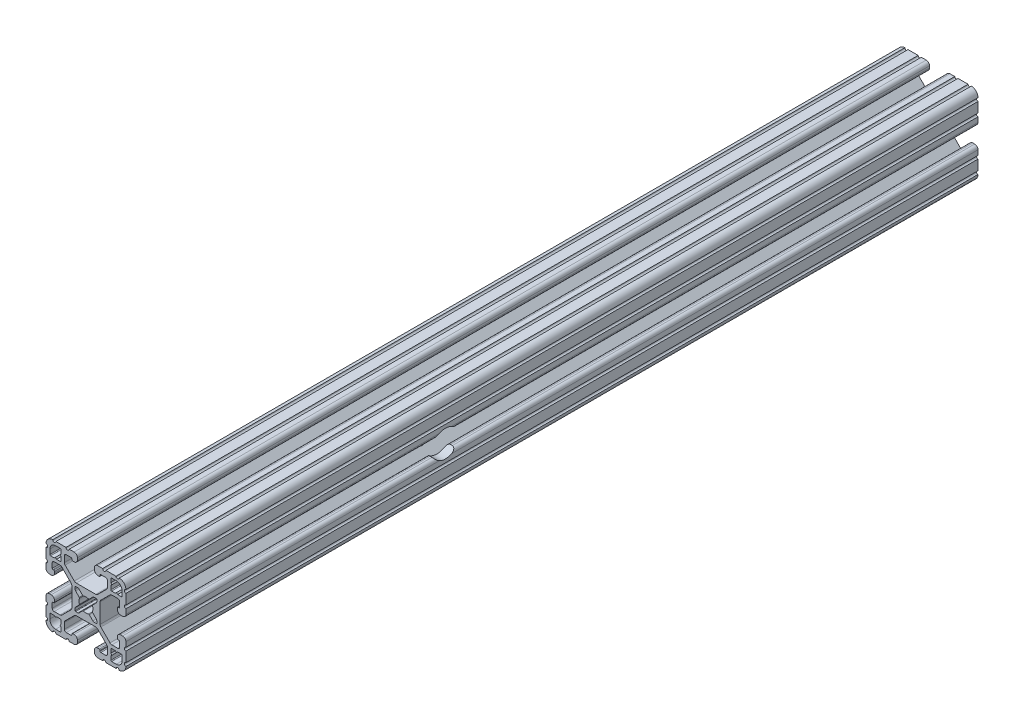
SolidWorks part; units mm, degrees
ref_plane "Front Plane" through (0, 0, 0) normal (0, 0, 1) x (1, 0, 0)
ref_plane "Top Plane" through (0, 0, 0) normal (0, 1, 0) x (1, 0, 0)
ref_plane "Right Plane" through (0, 0, 0) normal (1, 0, 0) x (0, 0, -1)
ref_plane "Plane1" through (0, 0, -2322.576) normal (0, 0, -1) x (-1, 0, 0)
sketch "Sketch1" plane through (0, 0, -2322.576) normal (0, 0, -1) x (-1, 0, 0)
  line L0 (17.2466, 14.4526) -> (17.2466, 12.2428)
  line L1 (16.8656, 11.8618) -> (15.0927, 11.8618)
  line L2 (15.0927, 11.8618) -> (14.5542, 12.4003)
  line L3 (14.5542, 12.4003) -> (14.0157, 11.8618)
  line L4 (14.0157, 11.8618) -> (12.2428, 11.8618)
  line L5 (11.8618, 12.2428) -> (11.8618, 14.0157)
  line L6 (11.8618, 14.0157) -> (12.4003, 14.5542)
  line L7 (12.4003, 14.5542) -> (11.8618, 15.0927)
  line L8 (11.8618, 15.0927) -> (11.8618, 16.8656)
  line L9 (12.2428, 17.2466) -> (14.4526, 17.2466)
  line L10 (17.2466, -12.2428) -> (17.2466, -14.4526)
  line L11 (14.4526, -17.2466) -> (12.2428, -17.2466)
  line L12 (11.8618, -16.8656) -> (11.8618, -15.0927)
  line L13 (11.8618, -15.0927) -> (12.4003, -14.5542)
  line L14 (12.4003, -14.5542) -> (11.8618, -14.0157)
  line L15 (11.8618, -14.0157) -> (11.8618, -12.2428)
  line L16 (12.2428, -11.8618) -> (14.0157, -11.8618)
  line L17 (14.0157, -11.8618) -> (14.5542, -12.4003)
  line L18 (14.5542, -12.4003) -> (15.0927, -11.8618)
  line L19 (15.0927, -11.8618) -> (16.8656, -11.8618)
  line L20 (5.1689, -3.9207) -> (5.1689, -4.9149)
  line L21 (4.9149, -5.1689) -> (3.9207, -5.1689)
  line L22 (3.2921, -4.9085) -> (1.5823, -3.1988)
  line L23 (-1.5823, -3.1988) -> (-3.2921, -4.9085)
  line L24 (-3.9207, -5.1689) -> (-4.9149, -5.1689)
  line L25 (-5.1689, -4.9149) -> (-5.1689, -3.9207)
  line L26 (-4.9085, -3.2921) -> (-3.1988, -1.5823)
  line L27 (-3.1988, 1.5823) -> (-4.9085, 3.2921)
  line L28 (-5.1689, 3.9207) -> (-5.1689, 4.9149)
  line L29 (-4.9149, 5.1689) -> (-3.9207, 5.1689)
  line L30 (-3.2921, 4.9085) -> (-1.5823, 3.1988)
  line L31 (1.5823, 3.1988) -> (3.2921, 4.9085)
  line L32 (3.9207, 5.1689) -> (4.9149, 5.1689)
  line L33 (5.1689, 4.9149) -> (5.1689, 3.9207)
  line L34 (4.9085, 3.2921) -> (3.1988, 1.5823)
  line L35 (3.1988, -1.5823) -> (4.9085, -3.2921)
  line L36 (-11.8618, -12.2428) -> (-11.8618, -14.0157)
  line L37 (-11.8618, -14.0157) -> (-12.4003, -14.5542)
  line L38 (-12.4003, -14.5542) -> (-11.8618, -15.0927)
  line L39 (-11.8618, -15.0927) -> (-11.8618, -16.8656)
  line L40 (-12.2428, -17.2466) -> (-14.4526, -17.2466)
  line L41 (-17.2466, -14.4526) -> (-17.2466, -12.2428)
  line L42 (-16.8656, -11.8618) -> (-15.0927, -11.8618)
  line L43 (-15.0927, -11.8618) -> (-14.5542, -12.4003)
  line L44 (-14.5542, -12.4003) -> (-14.0157, -11.8618)
  line L45 (-14.0157, -11.8618) -> (-12.2428, -11.8618)
  line L46 (-11.8618, 16.8656) -> (-11.8618, 15.0927)
  line L47 (-11.8618, 15.0927) -> (-12.4003, 14.5542)
  line L48 (-12.4003, 14.5542) -> (-11.8618, 14.0157)
  line L49 (-11.8618, 14.0157) -> (-11.8618, 12.2428)
  line L50 (-12.2428, 11.8618) -> (-14.0157, 11.8618)
  line L51 (-14.0157, 11.8618) -> (-14.5542, 12.4003)
  line L52 (-14.5542, 12.4003) -> (-15.0927, 11.8618)
  line L53 (-15.0927, 11.8618) -> (-16.8656, 11.8618)
  line L54 (-17.2466, 12.2428) -> (-17.2466, 14.4526)
  line L55 (-14.4526, 17.2466) -> (-12.2428, 17.2466)
  line L56 (19.05, -14.3256) -> (19.05, -9.4996)
  line L57 (19.05, -7.9756) -> (19.05, -5.6388)
  line L58 (17.4752, -4.064) -> (16.5608, -4.064)
  line L59 (14.986, -5.6388) -> (14.986, -6.35)
  line L60 (15.367, -6.731) -> (15.6972, -6.731)
  line L61 (16.0782, -7.112) -> (16.0782, -9.398)
  line L62 (15.1892, -10.287) -> (12.3756, -10.287)
  line L63 (11.4776, -9.915) -> (7.1157, -5.5531)
  line L64 (6.7437, -4.6551) -> (6.7437, 4.6551)
  line L65 (7.1157, 5.5531) -> (11.4776, 9.915)
  line L66 (12.3756, 10.287) -> (15.1892, 10.287)
  line L67 (16.0782, 9.398) -> (16.0782, 7.112)
  line L68 (15.6972, 6.731) -> (15.367, 6.731)
  line L69 (14.986, 6.35) -> (14.986, 5.6388)
  line L70 (16.5608, 4.064) -> (17.4752, 4.064)
  line L71 (19.05, 5.6388) -> (19.05, 7.9756)
  line L72 (19.05, 9.4996) -> (19.05, 14.3256)
  line L73 (14.3256, 19.05) -> (9.4996, 19.05)
  line L74 (7.9756, 19.05) -> (5.6388, 19.05)
  line L75 (4.064, 17.4752) -> (4.064, 16.5608)
  line L76 (5.6388, 14.986) -> (6.35, 14.986)
  line L77 (6.731, 15.367) -> (6.731, 15.6972)
  line L78 (7.112, 16.0782) -> (9.398, 16.0782)
  line L79 (10.287, 15.1892) -> (10.287, 12.3756)
  line L80 (9.915, 11.4776) -> (5.5531, 7.1157)
  line L81 (4.6551, 6.7437) -> (-4.6551, 6.7437)
  line L82 (-5.5531, 7.1157) -> (-9.915, 11.4776)
  line L83 (-10.287, 12.3756) -> (-10.287, 15.1892)
  line L84 (-9.398, 16.0782) -> (-7.112, 16.0782)
  line L85 (-6.731, 15.6972) -> (-6.731, 15.367)
  line L86 (-6.35, 14.986) -> (-5.6388, 14.986)
  line L87 (-4.064, 16.5608) -> (-4.064, 17.4752)
  line L88 (-5.6388, 19.05) -> (-7.9756, 19.05)
  line L89 (-9.4996, 19.05) -> (-14.3256, 19.05)
  line L90 (-19.05, 14.3256) -> (-19.05, 9.4996)
  line L91 (-19.05, 7.9756) -> (-19.05, 5.6388)
  line L92 (-17.4752, 4.064) -> (-16.5608, 4.064)
  line L93 (-14.986, 5.6388) -> (-14.986, 6.35)
  line L94 (-15.367, 6.731) -> (-15.6972, 6.731)
  line L95 (-16.0782, 7.112) -> (-16.0782, 9.398)
  line L96 (-15.1892, 10.287) -> (-12.3756, 10.287)
  line L97 (-11.4776, 9.915) -> (-7.1157, 5.5531)
  line L98 (-6.7437, 4.6551) -> (-6.7437, -4.6551)
  line L99 (-7.1157, -5.5531) -> (-11.4776, -9.915)
  line L100 (-12.3756, -10.287) -> (-15.1892, -10.287)
  line L101 (-16.0782, -9.398) -> (-16.0782, -7.112)
  line L102 (-15.6972, -6.731) -> (-15.367, -6.731)
  line L103 (-14.986, -6.35) -> (-14.986, -5.6388)
  line L104 (-16.5608, -4.064) -> (-17.4752, -4.064)
  line L105 (-19.05, -5.6388) -> (-19.05, -7.9756)
  line L106 (-19.05, -9.4996) -> (-19.05, -14.3256)
  line L107 (-14.3256, -19.05) -> (-9.4996, -19.05)
  line L108 (-7.9756, -19.05) -> (-5.6388, -19.05)
  line L109 (-4.064, -17.4752) -> (-4.064, -16.5608)
  line L110 (-5.6388, -14.986) -> (-6.35, -14.986)
  line L111 (-6.731, -15.367) -> (-6.731, -15.6972)
  line L112 (-7.112, -16.0782) -> (-9.398, -16.0782)
  line L113 (-10.287, -15.1892) -> (-10.287, -12.3756)
  line L114 (-9.915, -11.4776) -> (-5.5531, -7.1157)
  line L115 (-4.6551, -6.7437) -> (4.6551, -6.7437)
  line L116 (5.5531, -7.1157) -> (9.915, -11.4776)
  line L117 (10.287, -12.3756) -> (10.287, -15.1892)
  line L118 (9.398, -16.0782) -> (7.112, -16.0782)
  line L119 (6.731, -15.6972) -> (6.731, -15.367)
  line L120 (6.35, -14.986) -> (5.6388, -14.986)
  line L121 (4.064, -16.5608) -> (4.064, -17.4752)
  line L122 (5.6388, -19.05) -> (7.9756, -19.05)
  line L123 (9.4996, -19.05) -> (14.3256, -19.05)
  arc A0 (17.2466, 12.2428) -> (16.8656, 11.8618) centre (16.8656, 12.2428) cw
  arc A1 (12.2428, 11.8618) -> (11.8618, 12.2428) centre (12.2428, 12.2428) cw
  arc A2 (11.8618, 16.8656) -> (12.2428, 17.2466) centre (12.2428, 16.8656) cw
  arc A3 (14.4526, 17.2466) -> (17.2466, 14.4526) centre (14.4526, 14.4526) cw
  arc A4 (17.2466, -14.4526) -> (14.4526, -17.2466) centre (14.4526, -14.4526) cw
  arc A5 (12.2428, -17.2466) -> (11.8618, -16.8656) centre (12.2428, -16.8656) cw
  arc A6 (11.8618, -12.2428) -> (12.2428, -11.8618) centre (12.2428, -12.2428) cw
  arc A7 (16.8656, -11.8618) -> (17.2466, -12.2428) centre (16.8656, -12.2428) cw
  arc A8 (5.1689, -4.9149) -> (4.9149, -5.1689) centre (4.9149, -4.9149) cw
  arc A9 (3.9207, -5.1689) -> (3.2921, -4.9085) centre (3.9207, -4.2799) cw
  arc A10 (1.5823, -3.1988) -> (1.178, -3.1119) centre (1.3129, -3.4682) ccw
  arc A11 (1.178, -3.1119) -> (-1.178, -3.1119) centre (0, 0) cw
  arc A12 (-1.178, -3.1119) -> (-1.5823, -3.1988) centre (-1.3129, -3.4682) ccw
  arc A13 (-3.2921, -4.9085) -> (-3.9207, -5.1689) centre (-3.9207, -4.2799) cw
  arc A14 (-4.9149, -5.1689) -> (-5.1689, -4.9149) centre (-4.9149, -4.9149) cw
  arc A15 (-5.1689, -3.9207) -> (-4.9085, -3.2921) centre (-4.2799, -3.9207) cw
  arc A16 (-3.1988, -1.5823) -> (-3.1119, -1.178) centre (-3.4682, -1.3129) ccw
  arc A17 (-3.1119, -1.178) -> (-3.1119, 1.178) centre (0, 0) cw
  arc A18 (-3.1119, 1.178) -> (-3.1988, 1.5823) centre (-3.4682, 1.3129) ccw
  arc A19 (-4.9085, 3.2921) -> (-5.1689, 3.9207) centre (-4.2799, 3.9207) cw
  arc A20 (-5.1689, 4.9149) -> (-4.9149, 5.1689) centre (-4.9149, 4.9149) cw
  arc A21 (-3.9207, 5.1689) -> (-3.2921, 4.9085) centre (-3.9207, 4.2799) cw
  arc A22 (-1.5823, 3.1988) -> (-1.178, 3.1119) centre (-1.3129, 3.4682) ccw
  arc A23 (-1.178, 3.1119) -> (1.178, 3.1119) centre (0, 0) cw
  arc A24 (1.178, 3.1119) -> (1.5823, 3.1988) centre (1.3129, 3.4682) ccw
  arc A25 (3.2921, 4.9085) -> (3.9207, 5.1689) centre (3.9207, 4.2799) cw
  arc A26 (4.9149, 5.1689) -> (5.1689, 4.9149) centre (4.9149, 4.9149) cw
  arc A27 (5.1689, 3.9207) -> (4.9085, 3.2921) centre (4.2799, 3.9207) cw
  arc A28 (3.1988, 1.5823) -> (3.1119, 1.178) centre (3.4682, 1.3129) ccw
  arc A29 (3.1119, 1.178) -> (3.1119, -1.178) centre (0, 0) cw
  arc A30 (3.1119, -1.178) -> (3.1988, -1.5823) centre (3.4682, -1.3129) ccw
  arc A31 (4.9085, -3.2921) -> (5.1689, -3.9207) centre (4.2799, -3.9207) cw
  arc A32 (-11.8618, -16.8656) -> (-12.2428, -17.2466) centre (-12.2428, -16.8656) cw
  arc A33 (-14.4526, -17.2466) -> (-17.2466, -14.4526) centre (-14.4526, -14.4526) cw
  arc A34 (-17.2466, -12.2428) -> (-16.8656, -11.8618) centre (-16.8656, -12.2428) cw
  arc A35 (-12.2428, -11.8618) -> (-11.8618, -12.2428) centre (-12.2428, -12.2428) cw
  arc A36 (-12.2428, 17.2466) -> (-11.8618, 16.8656) centre (-12.2428, 16.8656) cw
  arc A37 (-11.8618, 12.2428) -> (-12.2428, 11.8618) centre (-12.2428, 12.2428) cw
  arc A38 (-16.8656, 11.8618) -> (-17.2466, 12.2428) centre (-16.8656, 12.2428) cw
  arc A39 (-17.2466, 14.4526) -> (-14.4526, 17.2466) centre (-14.4526, 14.4526) cw
  arc A40 (19.05, -9.4996) -> (19.05, -7.9756) centre (19.05, -8.7376) cw
  arc A41 (19.05, -5.6388) -> (17.4752, -4.064) centre (17.4752, -5.6388) ccw
  arc A42 (16.5608, -4.064) -> (14.986, -5.6388) centre (16.5608, -5.6388) ccw
  arc A43 (14.986, -6.35) -> (15.367, -6.731) centre (15.367, -6.35) ccw
  arc A44 (15.6972, -6.731) -> (16.0782, -7.112) centre (15.6972, -7.112) cw
  arc A45 (16.0782, -9.398) -> (15.1892, -10.287) centre (15.1892, -9.398) cw
  arc A46 (12.3756, -10.287) -> (11.4776, -9.915) centre (12.3756, -9.017) cw
  arc A47 (7.1157, -5.5531) -> (6.7437, -4.6551) centre (8.0137, -4.6551) cw
  arc A48 (6.7437, 4.6551) -> (7.1157, 5.5531) centre (8.0137, 4.6551) cw
  arc A49 (11.4776, 9.915) -> (12.3756, 10.287) centre (12.3756, 9.017) cw
  arc A50 (15.1892, 10.287) -> (16.0782, 9.398) centre (15.1892, 9.398) cw
  arc A51 (16.0782, 7.112) -> (15.6972, 6.731) centre (15.6972, 7.112) cw
  arc A52 (15.367, 6.731) -> (14.986, 6.35) centre (15.367, 6.35) ccw
  arc A53 (14.986, 5.6388) -> (16.5608, 4.064) centre (16.5608, 5.6388) ccw
  arc A54 (17.4752, 4.064) -> (19.05, 5.6388) centre (17.4752, 5.6388) ccw
  arc A55 (19.05, 7.9756) -> (19.05, 9.4996) centre (19.05, 8.7376) cw
  arc A56 (19.05, 14.3256) -> (19.0499, 15.8496) centre (19.05, 15.0876) cw
  arc A57 (19.0499, 15.8496) -> (15.8496, 19.0499) centre (15.875, 15.875) ccw
  arc A58 (15.8496, 19.0499) -> (14.3256, 19.05) centre (15.0876, 19.05) cw
  arc A59 (9.4996, 19.05) -> (7.9756, 19.05) centre (8.7376, 19.05) cw
  arc A60 (5.6388, 19.05) -> (4.064, 17.4752) centre (5.6388, 17.4752) ccw
  arc A61 (4.064, 16.5608) -> (5.6388, 14.986) centre (5.6388, 16.5608) ccw
  arc A62 (6.35, 14.986) -> (6.731, 15.367) centre (6.35, 15.367) ccw
  arc A63 (6.731, 15.6972) -> (7.112, 16.0782) centre (7.112, 15.6972) cw
  arc A64 (9.398, 16.0782) -> (10.287, 15.1892) centre (9.398, 15.1892) cw
  arc A65 (10.287, 12.3756) -> (9.915, 11.4776) centre (9.017, 12.3756) cw
  arc A66 (5.5531, 7.1157) -> (4.6551, 6.7437) centre (4.6551, 8.0137) cw
  arc A67 (-4.6551, 6.7437) -> (-5.5531, 7.1157) centre (-4.6551, 8.0137) cw
  arc A68 (-9.915, 11.4776) -> (-10.287, 12.3756) centre (-9.017, 12.3756) cw
  arc A69 (-10.287, 15.1892) -> (-9.398, 16.0782) centre (-9.398, 15.1892) cw
  arc A70 (-7.112, 16.0782) -> (-6.731, 15.6972) centre (-7.112, 15.6972) cw
  arc A71 (-6.731, 15.367) -> (-6.35, 14.986) centre (-6.35, 15.367) ccw
  arc A72 (-5.6388, 14.986) -> (-4.064, 16.5608) centre (-5.6388, 16.5608) ccw
  arc A73 (-4.064, 17.4752) -> (-5.6388, 19.05) centre (-5.6388, 17.4752) ccw
  arc A74 (-7.9756, 19.05) -> (-9.4996, 19.05) centre (-8.7376, 19.05) cw
  arc A75 (-14.3256, 19.05) -> (-15.8496, 19.0499) centre (-15.0876, 19.05) cw
  arc A76 (-15.8496, 19.0499) -> (-19.0499, 15.8496) centre (-15.875, 15.875) ccw
  arc A77 (-19.0499, 15.8496) -> (-19.05, 14.3256) centre (-19.05, 15.0876) cw
  arc A78 (-19.05, 9.4996) -> (-19.05, 7.9756) centre (-19.05, 8.7376) cw
  arc A79 (-19.05, 5.6388) -> (-17.4752, 4.064) centre (-17.4752, 5.6388) ccw
  arc A80 (-16.5608, 4.064) -> (-14.986, 5.6388) centre (-16.5608, 5.6388) ccw
  arc A81 (-14.986, 6.35) -> (-15.367, 6.731) centre (-15.367, 6.35) ccw
  arc A82 (-15.6972, 6.731) -> (-16.0782, 7.112) centre (-15.6972, 7.112) cw
  arc A83 (-16.0782, 9.398) -> (-15.1892, 10.287) centre (-15.1892, 9.398) cw
  arc A84 (-12.3756, 10.287) -> (-11.4776, 9.915) centre (-12.3756, 9.017) cw
  arc A85 (-7.1157, 5.5531) -> (-6.7437, 4.6551) centre (-8.0137, 4.6551) cw
  arc A86 (-6.7437, -4.6551) -> (-7.1157, -5.5531) centre (-8.0137, -4.6551) cw
  arc A87 (-11.4776, -9.915) -> (-12.3756, -10.287) centre (-12.3756, -9.017) cw
  arc A88 (-15.1892, -10.287) -> (-16.0782, -9.398) centre (-15.1892, -9.398) cw
  arc A89 (-16.0782, -7.112) -> (-15.6972, -6.731) centre (-15.6972, -7.112) cw
  arc A90 (-15.367, -6.731) -> (-14.986, -6.35) centre (-15.367, -6.35) ccw
  arc A91 (-14.986, -5.6388) -> (-16.5608, -4.064) centre (-16.5608, -5.6388) ccw
  arc A92 (-17.4752, -4.064) -> (-19.05, -5.6388) centre (-17.4752, -5.6388) ccw
  arc A93 (-19.05, -7.9756) -> (-19.05, -9.4996) centre (-19.05, -8.7376) cw
  arc A94 (-19.05, -14.3256) -> (-19.0499, -15.8496) centre (-19.05, -15.0876) cw
  arc A95 (-19.0499, -15.8496) -> (-15.8496, -19.0499) centre (-15.875, -15.875) ccw
  arc A96 (-15.8496, -19.0499) -> (-14.3256, -19.05) centre (-15.0876, -19.05) cw
  arc A97 (-9.4996, -19.05) -> (-7.9756, -19.05) centre (-8.7376, -19.05) cw
  arc A98 (-5.6388, -19.05) -> (-4.064, -17.4752) centre (-5.6388, -17.4752) ccw
  arc A99 (-4.064, -16.5608) -> (-5.6388, -14.986) centre (-5.6388, -16.5608) ccw
  arc A100 (-6.35, -14.986) -> (-6.731, -15.367) centre (-6.35, -15.367) ccw
  arc A101 (-6.731, -15.6972) -> (-7.112, -16.0782) centre (-7.112, -15.6972) cw
  arc A102 (-9.398, -16.0782) -> (-10.287, -15.1892) centre (-9.398, -15.1892) cw
  arc A103 (-10.287, -12.3756) -> (-9.915, -11.4776) centre (-9.017, -12.3756) cw
  arc A104 (-5.5531, -7.1157) -> (-4.6551, -6.7437) centre (-4.6551, -8.0137) cw
  arc A105 (4.6551, -6.7437) -> (5.5531, -7.1157) centre (4.6551, -8.0137) cw
  arc A106 (9.915, -11.4776) -> (10.287, -12.3756) centre (9.017, -12.3756) cw
  arc A107 (10.287, -15.1892) -> (9.398, -16.0782) centre (9.398, -15.1892) cw
  arc A108 (7.112, -16.0782) -> (6.731, -15.6972) centre (7.112, -15.6972) cw
  arc A109 (6.731, -15.367) -> (6.35, -14.986) centre (6.35, -15.367) ccw
  arc A110 (5.6388, -14.986) -> (4.064, -16.5608) centre (5.6388, -16.5608) ccw
  arc A111 (4.064, -17.4752) -> (5.6388, -19.05) centre (5.6388, -17.4752) ccw
  arc A112 (7.9756, -19.05) -> (9.4996, -19.05) centre (8.7376, -19.05) cw
  arc A113 (14.3256, -19.05) -> (15.8496, -19.0499) centre (15.0876, -19.05) cw
  arc A114 (15.8496, -19.0499) -> (19.0499, -15.8496) centre (15.875, -15.875) ccw
  arc A115 (19.0499, -15.8496) -> (19.05, -14.3256) centre (19.05, -15.0876) cw
extrude "Boss-Extrude1" add sketch "Sketch1" against normal blind 406.4
sketch "Sketch2" plane through (19.05, 0, 0) normal (1, 0, 0) x (0, 0, -1)
  line L1 (1916.176, 4.6551) -> (1916.176, -4.6551) construction
  line L2 (2043.176, 28.9936) -> (2043.176, -49.6002) construction
  circle A0 centre (2068.576, 0) radius 6.35
  dimension "D1" = 152.4
  dimension "D2" = 25.4
extrude "Cut-Extrude1" cut sketch "Sketch2" against normal through all and the other way through all
ref_plane "Plane2" through (19.05, 0, 0) normal (1, 0, 0) x (0, 0, -1)
sketch "Sketch4" plane through (19.05, 0, 0) normal (1, 0, 0) x (0, 0, -1)
  line L0 (1897.126, 19.0499) -> (1897.126, 228.5999) construction
  line L1 (2093.976, 0) -> (2093.976, 51.6785) construction
  line L2 (1897.126, 228.5999) -> (2192.401, 209.5499) construction
  line L3 (1897.126, 19.0499) -> (2106.0256, 19.0499) construction
  line L4 (1897.126, 247.6499) -> (2192.401, 247.6499) construction
  line L5 (1897.126, 228.5999) -> (2192.401, 228.5999) construction
  line L6 (2106.0256, 19.0499) -> (2131.2204, 47.6302) construction
  line L8 (1890.1123, 209.5499) -> (2192.401, 209.5499) construction
  arc A0 (2064.2572, 4.6551) -> (2064.2572, -4.6551) centre (2068.576, 0) ccw construction
  arc A1 (2192.401, 209.5499) -> (2042.2474, -29.2566) centre (1897.126, 228.5999) cw
  circle A2 centre (1897.126, 228.5999) radius 19.05
  dimension "D5" = 38.1
  dimension "D1" = 19.05
  dimension "D2" = 209.55
  dimension "D3" = 25.4
  dimension "D4" = 295.8889
  dimension "D6" = 19.05
  dimension "D7" = 295.275
  dimension "D8" = 208.8996
